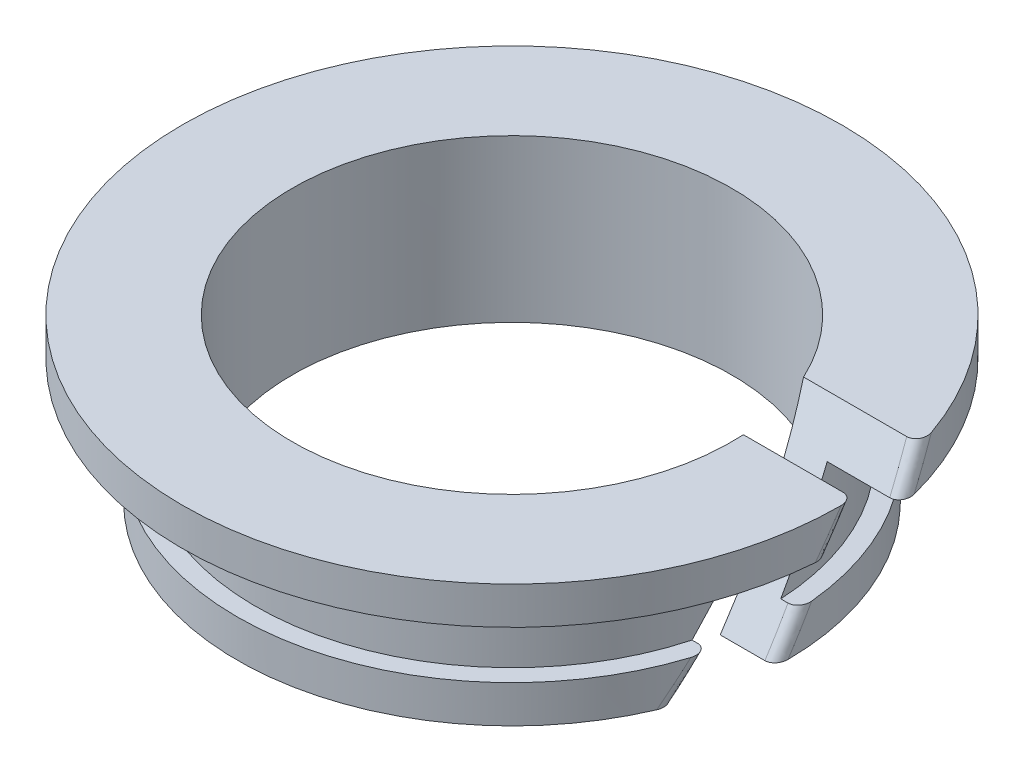
SolidWorks part; units mm, degrees
ref_plane "Front Plane" through (0, 0, 0) normal (0, 0, 1) x (1, 0, 0)
ref_plane "Top Plane" through (0, 0, 0) normal (0, 1, 0) x (1, 0, 0)
ref_plane "Right Plane" through (0, 0, 0) normal (1, 0, 0) x (0, 0, -1)
sketch "Sketch1" plane through (0, 0, 0) normal (0, 0, 1) x (1, 0, 0)
  line L0 (0, 18.7901) -> (0, 0) construction
  line L1 (4.7625, 0) -> (5.9531, 0)
  line L2 (5.9531, 0) -> (5.9531, 0.8128)
  line L3 (5.9531, 0.8128) -> (5.5563, 0.8128)
  line L4 (5.5563, 0.8128) -> (5.5563, 2.6924)
  line L5 (5.5563, 2.6924) -> (7.1438, 2.6924)
  line L6 (7.1438, 2.6924) -> (7.1438, 3.5052)
  line L7 (7.1438, 3.5052) -> (4.7625, 3.5052)
  line L8 (4.7625, 3.5052) -> (4.7625, 0)
  dimension "D1" = 9.525
  dimension "D2" = 11.1125
  dimension "D3" = 11.9062
  dimension "D4" = 14.2875
  dimension "D5" = 0.8128
  dimension "D6" = 0.8128
  dimension "D7" = 3.5052
revolve "Revolve1" add sketch "Sketch1" angle 360 about L0
sketch "Sketch2" plane through (0, 0, 0) normal (1, 0, 0) x (0, 0, -1)
  line L0 (0, 0) -> (0, 6.183) construction
  line L1 (7.1438, 3.5052) -> (-7.1438, 3.5052) construction
  line L2 (-5.9531, 0) -> (5.9531, 0) construction
  line L3 (1.996, 3.5052) -> (0.2612, 3.5052)
  line L4 (-1.9774, 0) -> (-0.2425, 0)
  line L5 (0.2612, 3.5052) -> (-1.9774, 0)
  line L6 (-0.2425, 0) -> (1.996, 3.5052)
extrude "Cut-Extrude1" cut sketch "Sketch2" along normal through all
fillet "Fillet1" radius 0.2286 4 edges at (5.9531, 0.4064, -0.017) (5.6994, 0.4036, 1.7196) (6.9292, 3.1007, -1.7377) (7.1437, 3.0988, -0.0016)
